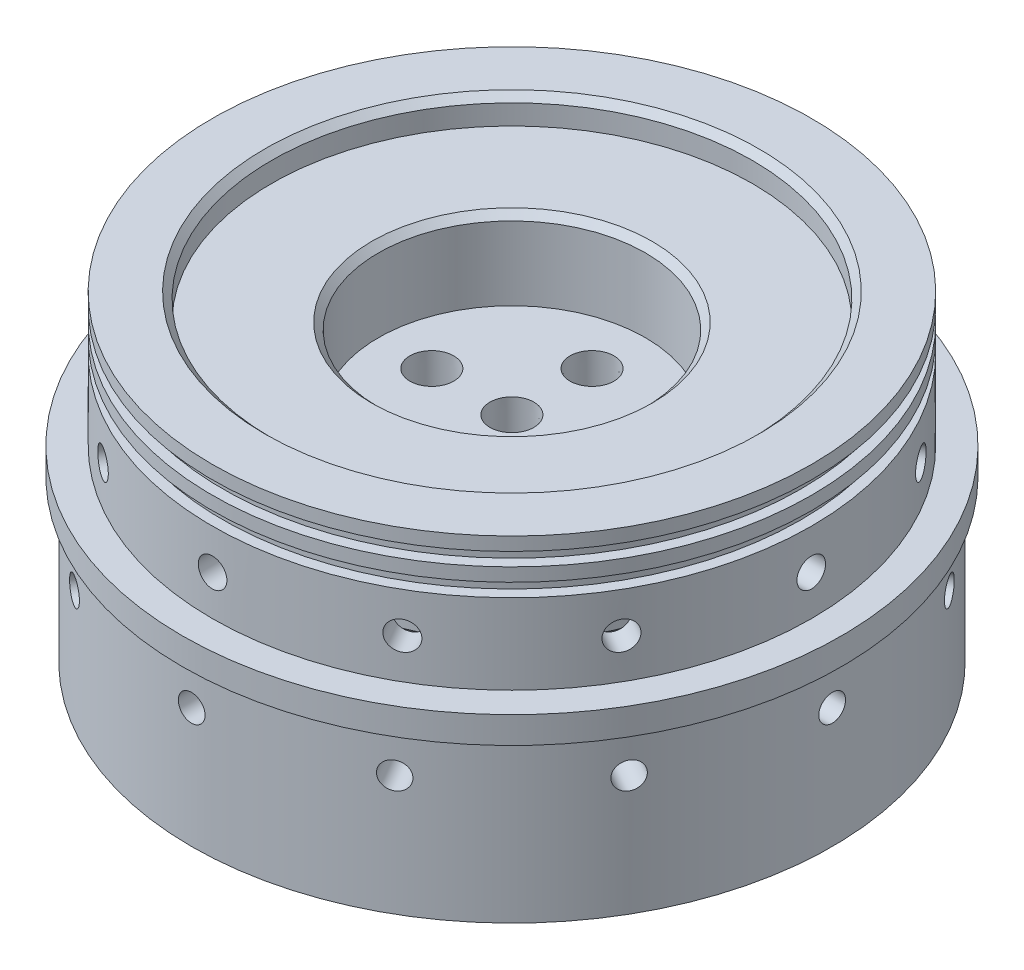
SolidWorks part; units mm, degrees
material "2024-T4"
ref_plane "Front Plane" through (0, 0, 0) normal (0, 0, 1) x (1, 0, 0)
ref_plane "Top Plane" through (0, 0, 0) normal (0, 1, 0) x (1, 0, 0)
ref_plane "Right Plane" through (0, 0, 0) normal (1, 0, 0) x (0, 0, -1)
sketch "Sketch1" plane through (0, 0, 0) normal (0, 1, 0) x (1, 0, 0)
  circle A0 centre (0, 0) radius 78.359
  dimension "D1" = 156.718
extrude "CenterRing(TotOD&Thk)" add sketch "Sketch1" along normal blind 6.35
sketch "Sketch2" plane through (0, 6.35, 0) normal (0, 1, 0) x (1, 0, 0)
  circle A0 centre (0, 0) radius 71.247
  dimension "D1" = 142.494
extrude "TankRing(TankID&Ht)" add sketch "Sketch2" along normal blind 31.75
sketch "Sketch3" plane through (0, 0, 0) normal (0, -1, 0) x (1, 0, 0)
  circle A0 centre (0, 0) radius 76.2
  dimension "D1" = 152.4
extrude "FbrGlsRing(FbrGlsID&Ht)" add sketch "Sketch3" along normal blind 38.1
sketch "Sketch4" plane through (0, -38.1, 0) normal (0, -1, 0) x (1, 0, 0)
  circle A0 centre (0, 0) radius 65.0875
  circle A1 centre (0, 0) radius 76.2 construction
  circle A2 centre (0, 0) radius 76.2
  dimension "D1" = 130.175
extrude "Wall&BlkhdThk" cut sketch "Sketch4" against normal offset from surface (60.325 mm away) 15.875 contours A0 up to face at (0, 38.1, 71.247)
sketch "Sketch5" plane through (0, 0, 0) normal (0, 0, 1) x (1, 0, 0)
  line L0 (71.247, 38.1) -> (-71.247, 38.1) construction
  line L1 (-71.247, 38.1) -> (-71.247, 6.35) construction
  line L2 (-71.247, 38.1) -> (-71.247, 6.35)
  line L3 (71.247, 38.1) -> (-71.247, 38.1)
  line L4 (-71.247, 34.925) -> (-68.707, 34.925)
  line L5 (-68.707, 34.925) -> (-68.707, 31.75)
  line L6 (-68.707, 31.75) -> (-71.247, 31.75)
  line L7 (-71.247, 28.575) -> (-68.707, 28.575)
  line L8 (-68.707, 28.575) -> (-68.707, 25.4)
  line L9 (-68.707, 25.4) -> (-71.247, 25.4)
  line L10 (0, 6.35) -> (0, 38.1) construction
  line L11 (78.359, 6.35) -> (-78.359, 6.35) construction
  dimension "D1" = 2.54
  dimension "D2" = 3.175
  dimension "D3" = 3.175
  dimension "D4" = 3.175
  dimension "D5" = 3.175
revolve "O-Ring Channel" cut sketch "Sketch5" angle 360 about L10
sketch "Sketch6" plane through (0, 0, 0) normal (0, 0, 1) x (1, 0, 0)
  line L0 (78.359, 6.35) -> (-78.359, 6.35) construction
  line L1 (78.359, 6.35) -> (-78.359, 6.35)
  circle A0 centre (0, 15.875) radius 3.4
  dimension "D1" = 6.8
  dimension "D2" = 9.525
extrude "TankBoltHole" cut sketch "Sketch6" against normal through all contours A0
pattern_circular "TankBoltCount" count 12 over 360 about axis through (0, 38.1, 0) along (0, -1, 0) of "TankBoltHole"
sketch "Sketch7" plane through (0, 0, 0) normal (0, 0, 1) x (1, 0, 0)
  line L0 (-76.2, 0) -> (76.2, 0) construction
  line L1 (-76.2, 0) -> (76.2, 0)
  circle A0 centre (0, -9.525) radius 3.175
  dimension "D1" = 6.35
  dimension "D2" = 9.525
extrude "FbrGlsBoltHole" cut sketch "Sketch7" against normal through all contours A0
pattern_circular "FbrGlsBoltCount" count 12 over 360 about axis through (0, -38.1, 0) along (0, 1, 0) of "FbrGlsBoltHole"
sketch "Sketch9" plane through (0, -38.1, 0) normal (0, -1, 0) x (1, 0, 0)
  circle A0 centre (0, 0) radius 71.4375
  circle A1 centre (0, 0) radius 76.2 construction
  circle A2 centre (0, 0) radius 76.2
  dimension "D1" = 4.7625
extrude "FbrGlsRingTrim" cut sketch "Sketch9" against normal blind 19.05 contours A0
sketch "Sketch10" plane through (0, 22.225, 0) normal (0, -1, 0) x (1, 0, 0)
  circle A0 centre (0, 0) radius 45.847
  dimension "D1" = 91.694
extrude "Boss-Extrude1" add sketch "Sketch10" along normal blind 25.4
sketch "Sketch12" plane through (0, 0, 0) normal (1, 0, 0) x (0, 0, -1)
  line L0 (-45.847, -3.175) -> (45.847, -3.175) construction
  line L1 (-45.847, 0.635) -> (-43.688, 0.635)
  line L2 (-45.847, 0.635) -> (-45.847, 7.747)
  line L3 (-45.847, 7.747) -> (-43.688, 7.747)
  line L4 (-42.926, 1.397) -> (-42.926, 6.985)
  line L5 (0, 0) -> (0, -3.175) construction
  arc A0 (-43.688, 0.635) -> (-42.926, 1.397) centre (-43.688, 1.397) ccw
  arc A1 (-43.688, 7.747) -> (-42.926, 6.985) centre (-43.688, 6.985) cw
  point P9 (-42.926, 0.635)
  point P12 (-42.926, 7.747)
  dimension "D5" = 0.762
  dimension "D1" = 3.81
  dimension "D2" = 45.847
  dimension "D3" = 7.112
  dimension "D4" = 42.926
revolve "Cut-Revolve1" cut sketch "Sketch12" angle 360 about L5
sketch "Sketch13" plane through (0, 38.1, 0) normal (0, 1, 0) x (1, 0, 0)
  circle A0 centre (0, 0) radius 57.15
  dimension "D1" = 114.3
extrude "Cut-Extrude1" cut sketch "Sketch13" against normal blind 6.35
sketch "Sketch14" plane through (0, 31.75, 0) normal (0, 1, 0) x (1, 0, 0)
  circle A0 centre (0, 0) radius 31.75
  dimension "D1" = 63.5
extrude "Cut-Extrude2" cut sketch "Sketch14" against normal blind 19.05
sketch "Sketch15" plane through (0, -3.175, 0) normal (0, -1, 0) x (1, 0, 0)
  point P0 (0, 0)
  point P1 (0, 19.05)
  point P6 (19.05, 0)
  point P7 (0, -19.05)
  point P8 (-19.05, 0)
  point P9 (0, 0)
  dimension "D1" = 19.05
  dimension "D2" = 4
hole_wizard "1/8 NPT Tapped Hole1" positions "Sketch18" profile "Sketch19" size "1/8" standard "ANSI Inch" end condition through all
sketch "Sketch18" plane through (0, -3.175, 0) normal (0, -1, 0) x (-1, 0, 0)
  point P0 (0, 0)
  point P4 (-19.05, 0)
  point P7 (0, -19.05)
  point P10 (0, 19.05)
  point P13 (19.05, 0)
sketch "Sketch19" plane through (0, -3.175, 0) normal (1, 0, 0) x (0, 0, -1)
  line L0 (0, 0) -> (0, 41.275)
  line L1 (0, 41.275) -> (4.2164, 41.275)
  line L2 (-4.9362, 25.4) -> (-5.6967, 0) construction
  line L3 (4.2164, 41.275) -> (4.2164, 25.4)
  line L4 (4.2164, 25.4) -> (4.9362, 25.4)
  line L5 (4.9362, 25.4) -> (5.6967, 0)
  line L7 (5.6967, 0) -> (0, 0)
  line L8 (0, -6.35) -> (0, 107.95) construction
  line L11 (-4.2164, 25.4) -> (-4.9362, 25.4) construction
  dimension "Thru Tap Drill Dia." = 8.4328
  dimension "Thru Tap Drill Depth" = 41.275
  dimension "Thread Dia." = 11.3934
  dimension "Thread Angle" = 3.43
  dimension "Thread Depth" = 25.4
chamfer "Chamfer1" distance 1.5875 angle 45 3 edges at (0, -3.175, -45.847) (0, 38.1, 57.15) (0, 31.75, 31.75)
ref_plane "Plane1" through (-45.847, 0, 0) normal (-1, 0, 0) x (0, 0, 1)
equation "\"D4@Sketch5\"=\"D2@Sketch5\""
equation "\"D5@Sketch5\"=\"D3@Sketch5\""
